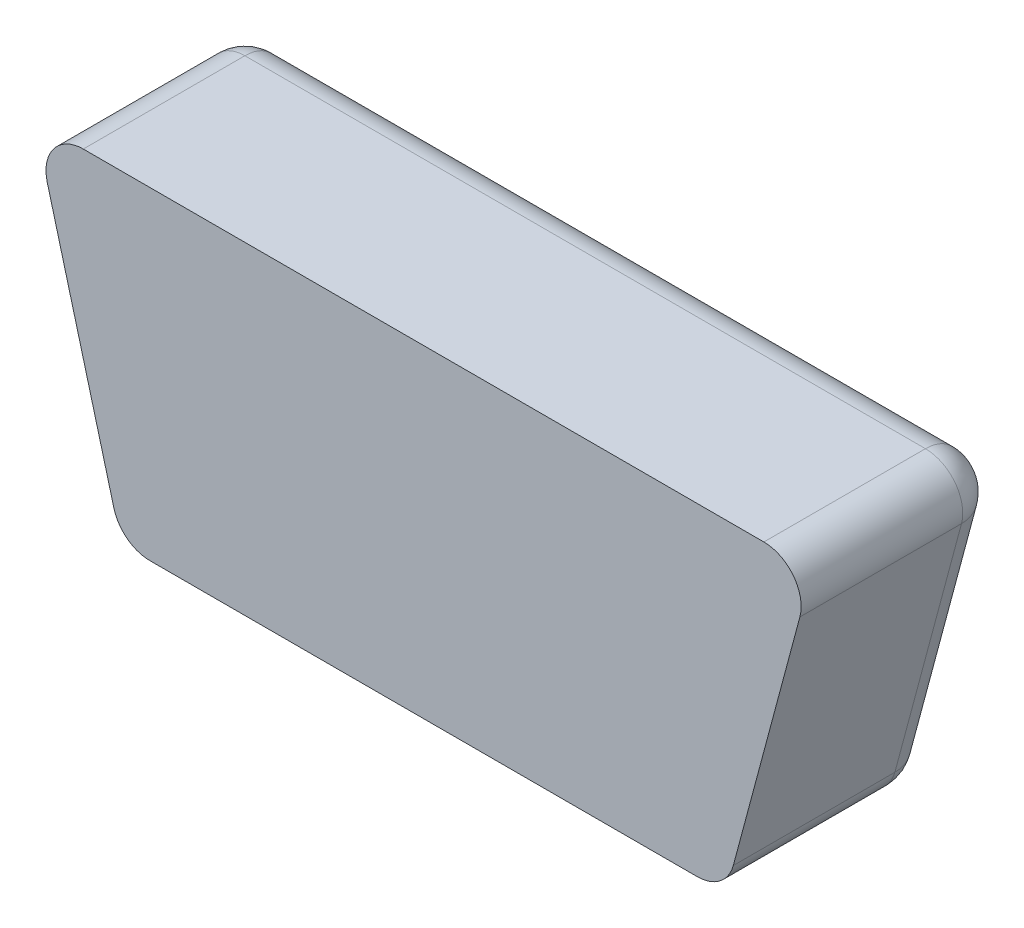
SolidWorks part; units mm, degrees
material "Резина"
ref_plane "Спереди" through (0, 0, 0) normal (0, 0, 1) x (1, 0, 0)
ref_plane "Сверху" through (0, 0, 0) normal (0, 1, 0) x (1, 0, 0)
ref_plane "Справа" through (0, 0, 0) normal (1, 0, 0) x (0, 0, -1)
sketch "Эскиз1" plane through (0, 0, 0) normal (0, 0, 1) x (1, 0, 0)
  line L0 (-6.08, -3.25) -> (6.08, -3.25)
  line L1 (6.08, -3.25) -> (7.8217, 3.25)
  line L2 (7.8217, 3.25) -> (-7.8217, 3.25)
  line L3 (-7.8217, 3.25) -> (-6.08, -3.25)
  point P2 (0, -3.25)
  point P5 (0, 3.25)
  point P8 (-6.9508, 0)
  point P10 (6.9508, 0)
  dimension "D1" = 12.16
  dimension "D2" = 6.5
  dimension "D3" = 30
extrude "Бобышка-Вытянуть1" add sketch "Эскиз1" along normal blind 4
fillet "Скругление1" radius 0.75 8 edges at (-7.8217, 3.25, 2) (-6.08, -3.25, 2) (-6.9508, 0, 0) (0, -3.25, 0) (6.08, -3.25, 2) (6.9508, 0, 0) (0, 3.25, 0) (7.8217, 3.25, 2)
